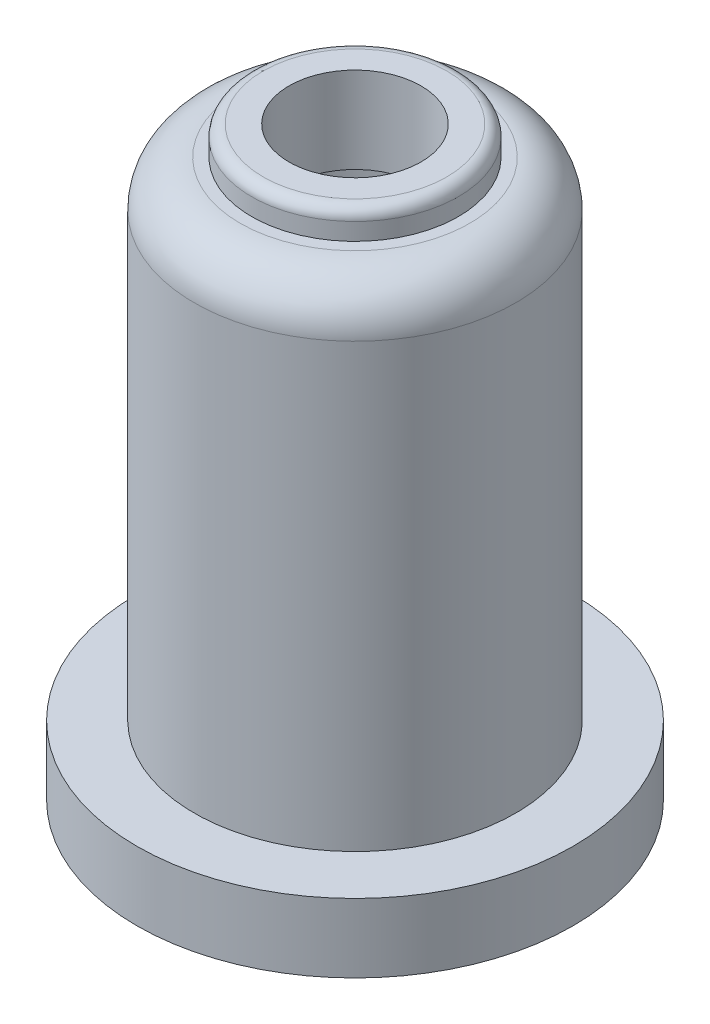
SolidWorks part; units mm, degrees
ref_plane "Ön Düzlem" through (0, 0, 0) normal (0, 0, 1) x (1, 0, 0)
ref_plane "Üst Düzlem" through (0, 0, 0) normal (0, 1, 0) x (1, 0, 0)
ref_plane "Sağ Düzlem" through (0, 0, 0) normal (1, 0, 0) x (0, 0, -1)
sketch "Çizim1" plane through (0, 0, 0) normal (0, 0, 1) x (1, 0, 0)
  line L0 (0, 0) -> (0, 109) construction
  line L1 (38, 0) -> (38, 12)
  line L2 (38, 0) -> (35, 0)
  line L3 (35, 0) -> (35, 3)
  line L4 (35, 3) -> (22, 3)
  line L5 (22, 3) -> (22, 29)
  line L6 (38, 12) -> (28, 12)
  line L7 (28, 12) -> (28, 89)
  line L8 (20, 31) -> (6, 31)
  line L9 (6, 31) -> (6, 41)
  line L10 (6, 41) -> (20, 41)
  line L11 (22, 43) -> (22, 85)
  line L12 (20, 97) -> (18, 97)
  line L13 (18, 97) -> (18, 100)
  line L14 (16, 102) -> (11.5, 102)
  line L15 (11.5, 102) -> (11.5, 87)
  line L16 (11.5, 87) -> (20, 87)
  arc A0 (28, 89) -> (20, 97) centre (20, 89) ccw
  arc A1 (22, 43) -> (20, 41) centre (20, 43) cw
  arc A2 (22, 29) -> (20, 31) centre (20, 29) ccw
  arc A3 (18, 100) -> (16, 102) centre (16, 100) ccw
  arc A4 (22, 85) -> (20, 87) centre (20, 85) ccw
  point P21 (28, 97)
  point P24 (22, 41)
  point P27 (22, 31)
  point P30 (18, 102)
  point P33 (22, 87)
  dimension "D17" = 8
  dimension "D18" = 2
  dimension "D1" = 109
  dimension "D2" = 12
  dimension "D3" = 38
  dimension "D4" = 3
  dimension "D5" = 3
  dimension "D6" = 13
  dimension "D7" = 28
  dimension "D8" = 10
  dimension "D9" = 85
  dimension "D10" = 16
  dimension "D11" = 10
  dimension "D12" = 46
  dimension "D13" = 22
  dimension "D14" = 10
  dimension "D15" = 5
  dimension "D16" = 6.5
revolve "Döndür1" add sketch "Çizim1" angle 360 about L0
